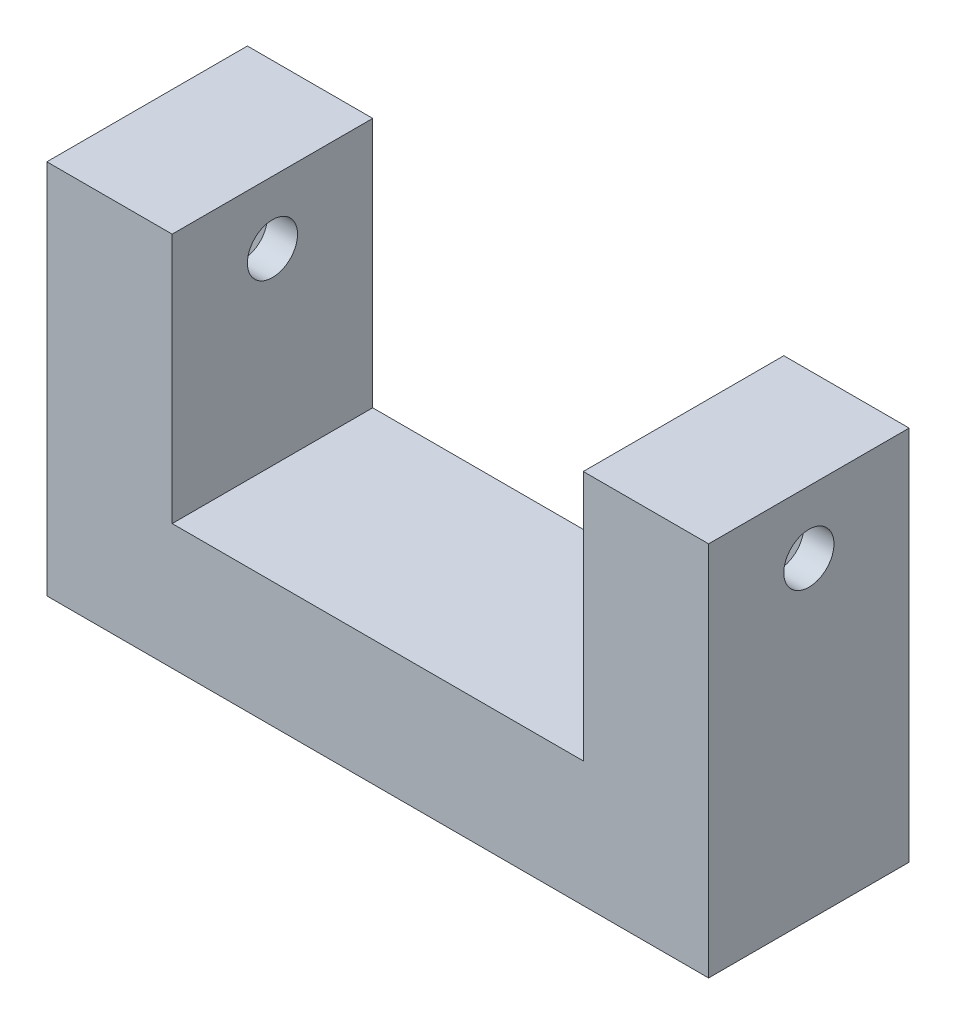
SolidWorks part; units mm, degrees
ref_plane "Спереди" through (0, 0, 0) normal (0, 0, 1) x (1, 0, 0)
ref_plane "Сверху" through (0, 0, 0) normal (0, 1, 0) x (1, 0, 0)
ref_plane "Справа" through (0, 0, 0) normal (1, 0, 0) x (0, 0, -1)
sketch "Эскиз2" plane through (0, 0, 0) normal (0, 0, 1) x (1, 0, 0)
  line L0 (0, 10) -> (-5, 10)
  line L1 (0, 0) -> (16.4, 0)
  line L2 (0, 0) -> (0, 10)
  line L3 (0, 10) -> (16.4, 10)
  line L4 (16.4, 0) -> (16.4, 10)
  line L5 (-5, 10) -> (-5, -5)
  line L6 (-5, -5) -> (21.4, -5)
  line L7 (21.4, -5) -> (21.4, 10)
  line L8 (21.4, 10) -> (16.4, 10)
  dimension "D1" = 16.4
  dimension "D2" = 10
  dimension "D3" = 5
  dimension "D4" = 5
  dimension "D5" = 5
extrude "Бобышка-Вытянуть1" add sketch "Эскиз2" along normal blind 8 contours L7 L8 L4 L1 L2 L0 L5 L6
sketch "Эскиз3" plane through (0, 10, 0) normal (0, 1, 0) x (1, 0, 0)
  line L0 (-5, -4) -> (21.4, -4) construction
  line L1 (-5, -8) -> (-5, 0) construction
  line L2 (21.4, -8) -> (21.4, 0) construction
  line L3 (-2.5, 0) -> (-2.5, -8) construction
  line L6 (0, 0) -> (-5, 0) construction
  line L7 (0, -8) -> (-5, -8) construction
  line L8 (18.9, 0) -> (18.9, -8) construction
  line L9 (21.4, 0) -> (16.4, 0) construction
  line L10 (21.4, -8) -> (16.4, -8) construction
  line L12 (-3.8, -1.65) -> (-1.2, -1.65)
  line L13 (-3.8, -1.65) -> (-3.8, -6.35)
  line L14 (-3.8, -6.35) -> (-1.2, -6.35)
  line L15 (-1.2, -1.65) -> (-1.2, -6.35)
  line L16 (-3.8, -1.65) -> (-1.2, -6.35) construction
  line L17 (-3.8, -6.35) -> (-1.2, -1.65) construction
  line L18 (17.6, -1.65) -> (20.2, -1.65)
  line L19 (17.6, -1.65) -> (17.6, -6.35)
  line L20 (17.6, -6.35) -> (20.2, -6.35)
  line L21 (20.2, -1.65) -> (20.2, -6.35)
  line L22 (17.6, -1.65) -> (20.2, -6.35) construction
  line L23 (17.6, -6.35) -> (20.2, -1.65) construction
  point P18 (-2.5, -4)
  point P23 (18.9, -4)
  dimension "D1" = 4.7
  dimension "D2" = 2.6
  dimension "D3" = 2.6
  dimension "D4" = 4.7
extrude "Вырез-Вытянуть1" cut sketch "Эскиз3" against normal through all from offset 1 offset against normal yes
sketch "Эскиз4" plane through (21.4, 0, 0) normal (1, 0, 0) x (0, 0, -1)
  line L0 (-4, 10) -> (-4, -5) construction
  line L1 (-8, 10) -> (0, 10) construction
  line L2 (-8, -5) -> (0, -5) construction
  circle A0 centre (-4, 7.5) radius 1
  dimension "D2" = 2
  dimension "D1" = 2.5
extrude "Вырез-Вытянуть2" cut sketch "Эскиз4" against normal through all
chamfer "Фаска1" distance 0.2 angle 45 8 edges at (-2.5, -5, 6.35) (-3.8, -5, 4) (-2.5, -5, 1.65) (-1.2, -5, 4) (18.9, -5, 6.35) (17.6, -5, 4) (20.2, -5, 4) (18.9, -5, 1.65)
